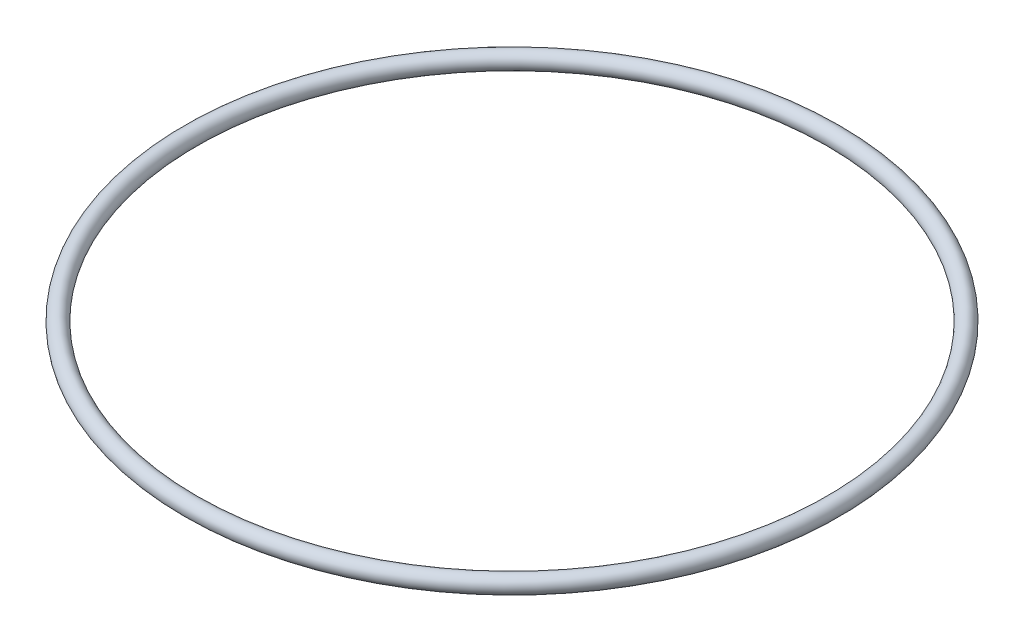
SolidWorks part; units mm, degrees
material "Gummi"
ref_plane "Front Plane" through (0, 0, 0) normal (0, 0, 1) x (1, 0, 0)
ref_plane "Top Plane" through (0, 0, 0) normal (0, 1, 0) x (1, 0, 0)
ref_plane "Right Plane" through (0, 0, 0) normal (1, 0, 0) x (0, 0, -1)
sketch "Sketch1" plane through (0, 0, 0) normal (0, 0, 1) x (1, 0, 0)
  line L0 (0, 0) -> (0, 13.4289) construction
  circle A0 centre (38, 0) radius 1
  dimension "D1" = 2
  dimension "D2" = 38
revolve "Revolve1" add sketch "Sketch1" angle 360 about L0
